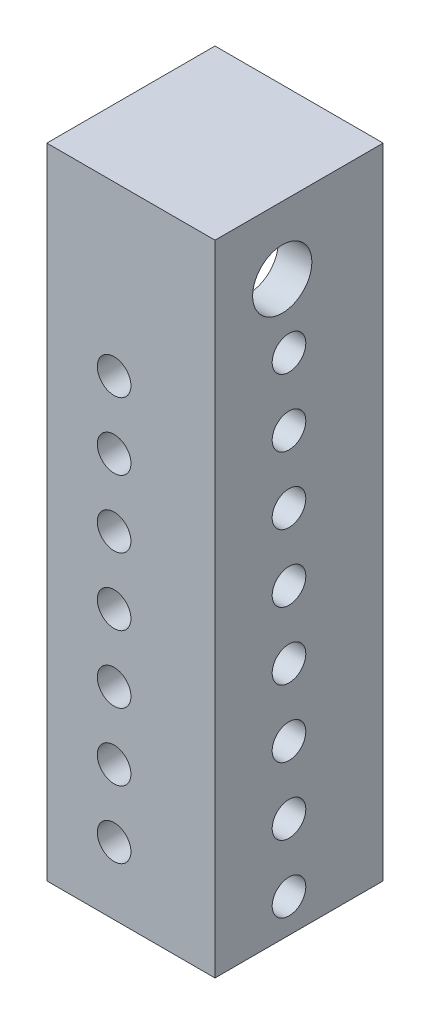
SolidWorks part; units mm, degrees
material "PET"
ref_plane "Front Plane" through (0, 0, 0) normal (0, 0, 1) x (1, 0, 0)
ref_plane "Top Plane" through (0, 0, 0) normal (0, 1, 0) x (1, 0, 0)
ref_plane "Right Plane" through (0, 0, 0) normal (1, 0, 0) x (0, 0, -1)
sketch "Sketch2" plane through (0, 0, 0) normal (0, 1, 0) x (1, 0, 0)
  line L1 (-41.3514, 38.3779) -> (22.1486, 38.3779)
  line L2 (-41.3514, 38.3779) -> (-41.3514, -25.1221)
  line L3 (-41.3514, -25.1221) -> (22.1486, -25.1221)
  line L4 (22.1486, 38.3779) -> (22.1486, -25.1221)
  dimension "D1" = 63.5
  dimension "D2" = 63.5
extrude "Boss-Extrude1" add sketch "Sketch2" along normal blind 241.3
ref_plane "Plane1" through (0, 101.6, 0) normal (0, 1, 0) x (1, 0, 0)
sketch "Sketch4" plane through (0, 101.6, 0) normal (0, 1, 0) x (1, 0, 0)
  line L0 (22.1486, -25.1221) -> (22.1486, 38.3779) construction
  line L1 (-41.3514, 38.3779) -> (9.4486, 38.3779)
  line L2 (-41.3514, 38.3779) -> (-41.3514, -12.4221)
  line L3 (-41.3514, -12.4221) -> (9.4486, -12.4221)
  line L4 (9.4486, 38.3779) -> (9.4486, -12.4221)
  line L5 (-41.3514, -25.1221) -> (22.1486, -25.1221) construction
  dimension "D1" = 12.7
  dimension "D2" = 12.7
extrude "Cut-Extrude1" cut sketch "Sketch4" along normal mid plane 190.5
sketch "Sketch5" plane through (0, 0, 25.1221) normal (0, 0, 1) x (1, 0, 0)
  line L1 (-41.3514, 0) -> (22.1486, 0) construction
  line L3 (-41.3514, 241.3) -> (-41.3514, 0) construction
  circle A4 centre (-15.9514, 25.4) radius 6.35
  circle A5 centre (-15.9514, 50.8) radius 6.35
  circle A6 centre (-15.9514, 76.2) radius 6.35
  circle A7 centre (-15.9514, 101.6) radius 6.35
  circle A8 centre (-15.9514, 127) radius 6.35
  circle A9 centre (-15.9514, 152.4) radius 6.35
  circle A10 centre (-15.9514, 177.8) radius 6.35
  dimension "D1" = 25.4
  dimension "D4" = 12.7
  dimension "D3" = 25.4
  dimension "D2" = 7
extrude "Cut-Extrude2" cut sketch "Sketch5" against normal through all
sketch "Sketch6" plane through (22.1486, 0, 0) normal (1, 0, 0) x (0, 0, -1)
  line L2 (38.3779, 241.3) -> (38.3779, 0) construction
  line L3 (-25.1221, 0) -> (38.3779, 0) construction
  circle A4 centre (2.8179, 12.7) radius 6.35
  circle A5 centre (2.8179, 38.1) radius 6.35
  circle A6 centre (2.8179, 63.5) radius 6.35
  circle A7 centre (2.8179, 88.9) radius 6.35
  circle A8 centre (2.8179, 114.3) radius 6.35
  circle A11 centre (2.8179, 139.7) radius 6.35
  circle A12 centre (2.8179, 165.1) radius 6.35
  circle A13 centre (2.8179, 190.5) radius 6.35
  dimension "D1" = 35.56
  dimension "D4" = 12.7
  dimension "D2" = 12.7
  dimension "D3" = 8
extrude "Cut-Extrude3" cut sketch "Sketch6" against normal up to surface (12.7 mm away) up to face at (9.4486, 101.6, -12.9779)
sketch "Sketch7" plane through (0, 6.35, 0) normal (0, 1, 0) x (1, 0, 0)
  line L0 (22.1486, -25.1221) -> (22.1486, 38.3779) construction
  line L1 (-41.3514, 38.3779) -> (9.4486, 38.3779)
  line L2 (-41.3514, 38.3779) -> (-41.3514, -12.4221)
  line L3 (-41.3514, -12.4221) -> (-3.2514, -12.4221)
  line L4 (9.4486, 38.3779) -> (9.4486, 0.2779)
  line L5 (-41.3514, -25.1221) -> (22.1486, -25.1221) construction
  line L6 (9.4486, 0.2779) -> (9.4486, -12.4221)
  line L7 (9.4486, -12.4221) -> (-3.2514, -12.4221)
  dimension "D1" = 12.7
  dimension "D2" = 12.7
extrude "Cut-Extrude4" cut sketch "Sketch7" against normal through all
ref_plane "Plane2" through (0, 228.6, 0) normal (0, 1, 0) x (1, 0, 0)
sketch "Sketch34" plane through (0, 196.85, 0) normal (0, -1, 0) x (1, 0, 0)
  line L0 (-3.2514, 12.4221) -> (9.4486, 12.4221)
  line L1 (-41.3514, 12.4221) -> (-3.2514, 12.4221)
  line L2 (-41.3514, 12.4221) -> (-41.3514, -38.3779)
  line L3 (-41.3514, -38.3779) -> (9.4486, -38.3779)
  line L4 (9.4486, -0.2779) -> (9.4486, -38.3779)
  line L5 (9.4486, 12.4221) -> (9.4486, -0.2779)
extrude "Cut-Extrude6" cut sketch "Sketch34" against normal up to surface (31.75 mm away)
sketch "Sketch37" plane through (0, 228.6, 0) normal (0, 1, 0) x (1, 0, 0)
  line L0 (22.1486, -25.1221) -> (22.1486, 38.3779) construction
  line L1 (-36.5254, -2.2621) -> (-27.6354, -2.2621)
  line L2 (-36.5254, -2.2621) -> (-36.5254, 7.8979)
  line L3 (-36.5254, 7.8979) -> (-27.6354, 7.8979)
  line L4 (-27.6354, -2.2621) -> (-27.6354, 7.8979)
  line L5 (-19.7614, -2.2621) -> (-10.8714, -2.2621)
  line L6 (-19.7614, -2.2621) -> (-19.7614, 7.8979)
  line L7 (-19.7614, 7.8979) -> (-10.8714, 7.8979)
  line L8 (-10.8714, -2.2621) -> (-10.8714, 7.8979)
  line L9 (22.1486, 38.3779) -> (-41.3514, 38.3779) construction
  dimension "D1" = 10.16
  dimension "D2" = 8.89
  dimension "D3" = 7.874
  dimension "D4" = 33.02
  dimension "D5" = 30.48
extrude "Boss-Extrude3" add sketch "Sketch37" against normal blind 10.16
sketch "Sketch38" plane through (-36.5254, 0, 0) normal (-1, 0, 0) x (0, 0, 1)
  line L0 (-7.8979, 218.44) -> (2.2621, 218.44) construction
  line L1 (2.2621, 218.44) -> (2.2621, 228.6) construction
  circle A0 centre (-2.8179, 223.52) radius 2.032
  dimension "D1" = 5.08
  dimension "D2" = 5.08
extrude "Cut-Extrude8" cut sketch "Sketch38" against normal up to surface (58.674 mm away) up to face at (22.1486, 190.5, -9.1679)
fillet "Fillet4" radius 3.81 4 edges at (-15.3164, 218.44, -7.8979) (-15.3164, 218.44, 2.2621) (-32.0804, 218.44, 2.2621) (-32.0804, 218.44, -7.8979)
sketch "Sketch39" plane through (0, 0, 0) normal (0, 1, 0) x (1, 0, 0)
  line L0 (22.1486, -25.1221) -> (22.1486, 38.3779) construction
  line L1 (-41.3514, -25.1221) -> (22.1486, -25.1221)
  line L2 (-41.3514, -25.1221) -> (-41.3514, 38.3779)
  line L3 (-41.3514, 38.3779) -> (22.1486, 38.3779)
  line L4 (22.1486, -25.1221) -> (22.1486, 38.3779)
  line L5 (22.1486, 38.3779) -> (9.4486, 38.3779) construction
sketch "Sketch40" plane through (22.1486, 0, 0) normal (1, 0, 0) x (0, 0, -1)
  line L0 (-25.1221, 241.3) -> (38.3779, 241.3) construction
  line L2 (38.3779, 241.3) -> (38.3779, 31.75) construction
  circle A0 centre (0.2779, 215.9) radius 11.176
  dimension "D1" = 25.4
  dimension "D2" = 38.1
extrude "Cut-Extrude10" cut sketch "Sketch40" against normal blind 12.7
